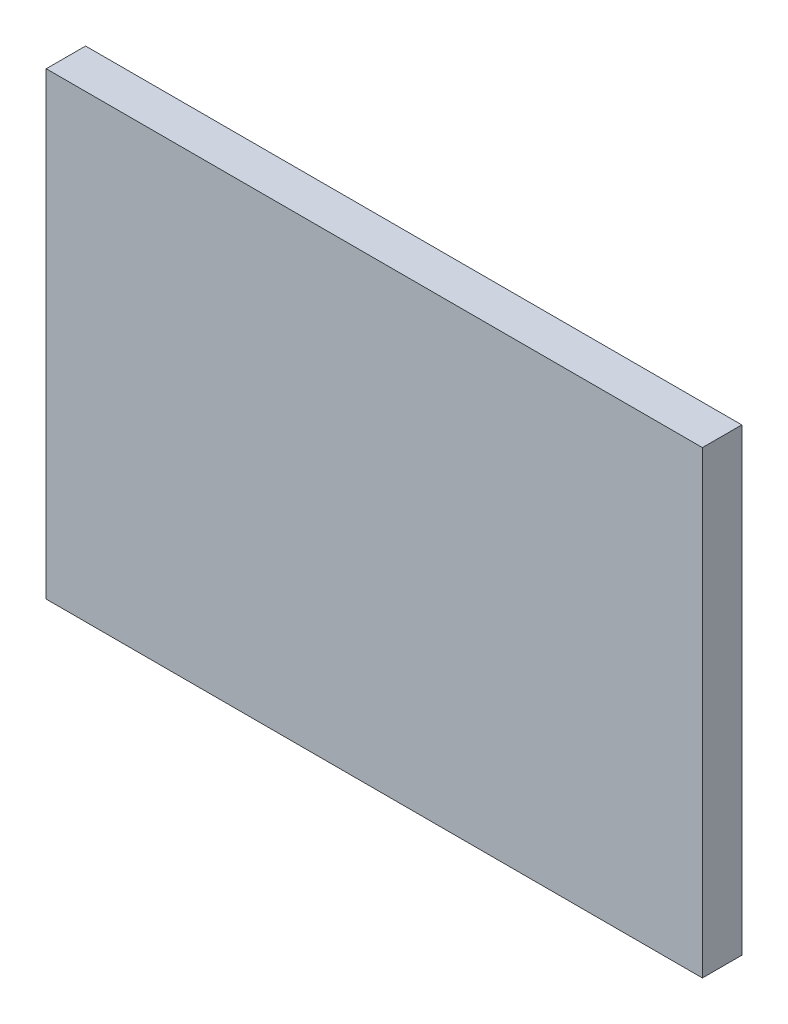
SolidWorks part; units mm, degrees
material "Glass"
ref_plane "Front Plane" through (0, 0, 0) normal (0, 0, 1) x (1, 0, 0)
ref_plane "Top Plane" through (0, 0, 0) normal (0, 1, 0) x (1, 0, 0)
ref_plane "Right Plane" through (0, 0, 0) normal (1, 0, 0) x (0, 0, -1)
sketch "Sketch1" plane through (0, 0, 0) normal (0, 0, 1) x (1, 0, 0)
  line L1 (-25, 17.5) -> (25, 17.5)
  line L2 (-25, 17.5) -> (-25, -17.5)
  line L3 (-25, -17.5) -> (25, -17.5)
  line L4 (25, 17.5) -> (25, -17.5)
  line L5 (-25, 17.5) -> (25, -17.5) construction
  line L6 (-25, -17.5) -> (25, 17.5) construction
  point P0 (0, 0)
  dimension "D1" = 50
  dimension "D2" = 35
extrude "Boss-Extrude1" add sketch "Sketch1" along normal blind 3
